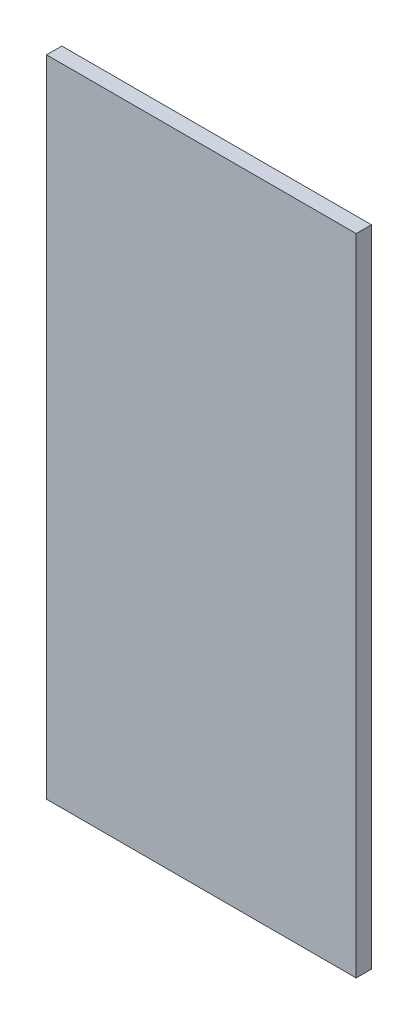
SolidWorks part; units mm, degrees
ref_plane "Front Plane" through (0, 0, 0) normal (0, 0, 1) x (1, 0, 0)
ref_plane "Top Plane" through (0, 0, 0) normal (0, 1, 0) x (1, 0, 0)
ref_plane "Right Plane" through (0, 0, 0) normal (1, 0, 0) x (0, 0, -1)
sketch "Sketch1" plane through (0, 0, 0) normal (0, 0, 1) x (1, 0, 0)
  line L1 (182.5, -380) -> (-182.5, -380)
  line L2 (182.5, -380) -> (182.5, 380)
  line L3 (182.5, 380) -> (-182.5, 380)
  line L4 (-182.5, -380) -> (-182.5, 380)
  line L5 (182.5, -380) -> (-182.5, 380) construction
  line L6 (182.5, 380) -> (-182.5, -380) construction
  point P0 (0, 0)
  dimension "D1" = 760
  dimension "D2" = 365
extrude "Boss-Extrude1" add sketch "Sketch1" along normal blind 18
equation "\"H_DSP\"=18"
equation "\"D1@Boss-Extrude1\"=\"H_DSP\""
